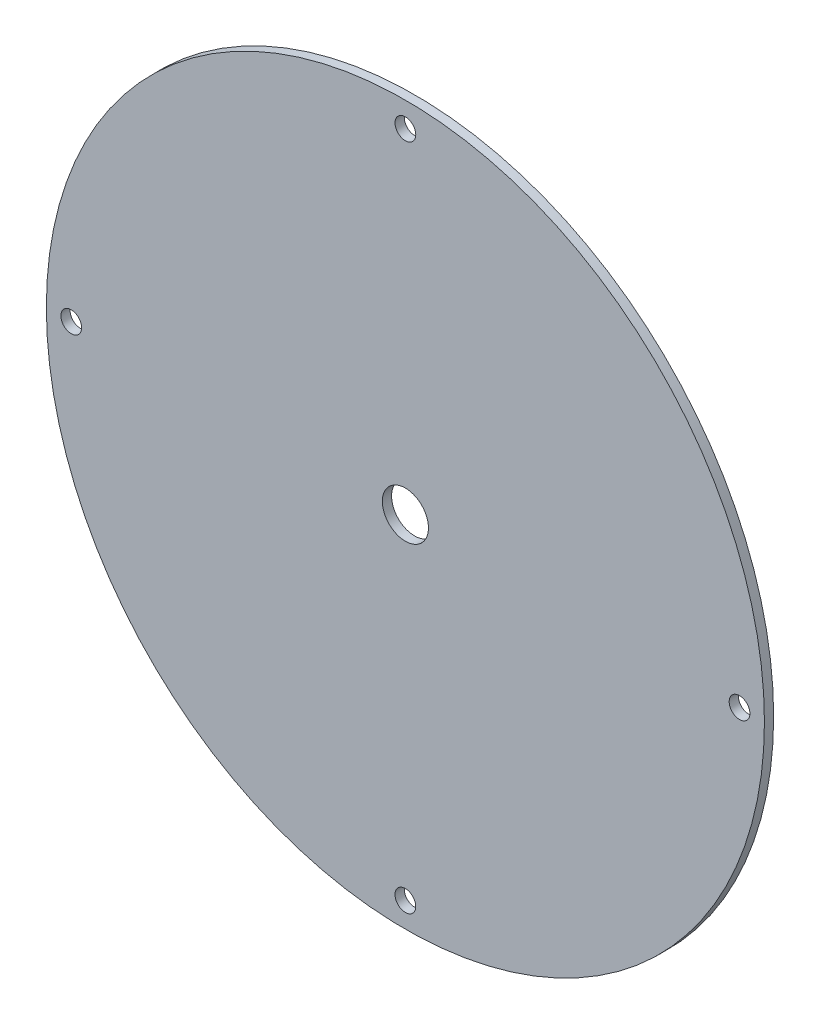
SolidWorks part; units mm, degrees
material "Acrylique (impact moyen-haut)"
ref_plane "Plan de face" through (0, 0, 0) normal (0, 0, 1) x (1, 0, 0)
ref_plane "Plan de dessus" through (0, 0, 0) normal (0, 1, 0) x (1, 0, 0)
ref_plane "Plan de droite" through (0, 0, 0) normal (1, 0, 0) x (0, 0, -1)
sketch "Esquisse1" plane through (0, 0, 0) normal (0, 0, 1) x (1, 0, 0)
  line L0 (0.0711, 73.0176) -> (0.0711, -71.9824) construction
  line L1 (-72.4289, 0.5176) -> (72.5711, 0.5176) construction
  circle A0 centre (0.0711, 0.5176) radius 77.9
  circle A1 centre (0.0711, 0.5176) radius 72.5 construction
  circle A2 centre (0.0711, 73.0176) radius 2.25
  circle A3 centre (72.5711, 0.5176) radius 2.25
  circle A4 centre (0.0711, -71.9824) radius 2.25
  circle A5 centre (-72.4289, 0.5176) radius 2.25
  circle A7 centre (0.0711, 0.5176) radius 5
  point P0 (0.0711, 0.5176)
  point P16 (0.0711, 0.5176)
  point P17 (0.0711, 0.5176)
  point P18 (0.0711, 0.5176)
  point P19 (0.0711, 0.5176)
  point P20 (0.0711, 0.5176)
  dimension "D1" = 155.8
  dimension "D2" = 145
  dimension "D3" = 4.5
  dimension "D5" = 10
extrude "Boss.-Extru.1" add sketch "Esquisse1" along normal blind 2
